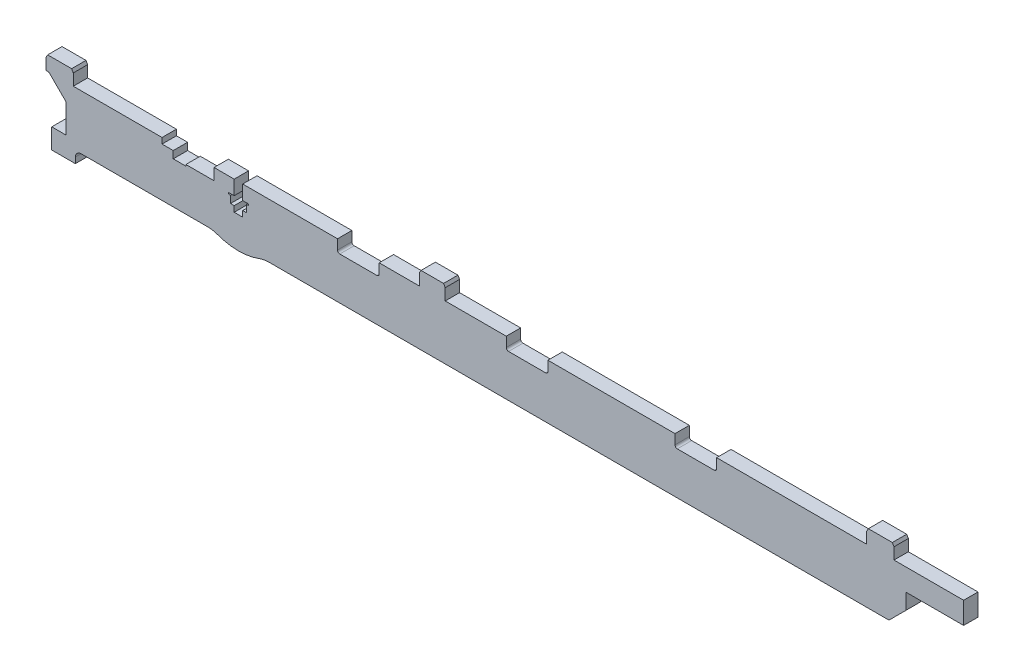
SolidWorks part; units mm, degrees
material "6061-T6 Black anodised"
ref_plane "Front Plane" through (0, 0, 0) normal (0, 0, 1) x (1, 0, 0)
ref_plane "Top Plane" through (0, 0, 0) normal (0, 1, 0) x (1, 0, 0)
ref_plane "Right Plane" through (0, 0, 0) normal (1, 0, 0) x (0, 0, -1)
sketch "Sketch1" plane through (0, 0, 0) normal (0, 0, 1) x (1, 0, 0)
  line L0 (-250.8, 3.6) -> (-241, 3.6)
  line L1 (0, 0) -> (20, 0)
  line L2 (-232.5, 8.6) -> (-232.5, -2.4) construction
  line L3 (-4.25, 7.6) -> (20, 7.6)
  line L4 (20, 0) -> (20, 7.6)
  line L5 (-13.75, 7.6) -> (-66, 7.6)
  line L6 (0, 0) -> (0, -11.4)
  line L7 (0, -11.4) -> (-221.7995, -11.4)
  line L8 (-292.5, 1.6) -> (-292.5, -8.4)
  line L9 (-259.0932, 7.6) -> (-290, 7.6)
  line L10 (-299.5, 7.6) -> (-299.5, 12.6)
  line L11 (-299.5, 12.6) -> (-290, 12.6)
  line L12 (-290, 7.6) -> (-290, 12.6)
  line L13 (-169.5, 7.6) -> (-169.5, 12.6)
  line L14 (-250.8, 3.6) -> (-250.8, 3.1)
  line L15 (-250.8, 3.1) -> (-255.2, 3.1)
  line L16 (-255.2, 3.1) -> (-255.2, 5.6)
  line L17 (-255.2, 5.6) -> (-259.0932, 5.6)
  line L18 (-4.25, 7.6) -> (-4.25, 12.6)
  line L19 (-4.25, 12.6) -> (-13.75, 12.6)
  line L20 (-13.75, 7.6) -> (-13.75, 12.6)
  line L21 (-259.0932, 5.6) -> (-259.0932, 7.6)
  line L22 (-255, 3.6) -> (-251, 3.6) construction
  line L23 (-255, 3.6) -> (-255, 13.6) construction
  line L24 (-251, 3.6) -> (-251, 13.6) construction
  line L25 (-255, 13.6) -> (-251, 13.6) construction
  line L26 (-255, 3.6) -> (-251, 13.6) construction
  line L27 (-271, 32.6) -> (-219.2068, 32.6) construction
  line L28 (-271, 32.6) -> (-271, 13.6) construction
  line L29 (-250, 33.6) -> (-250, 13.6) construction
  line L30 (-271, 13.6) -> (-250, 13.6) construction
  line L31 (-271, 32.6) -> (-250, 13.6) construction
  line L32 (-250, 33.6) -> (-271, 13.6) construction
  line L33 (-169.5, 12.6) -> (-160.5, 12.6)
  line L34 (-160.5, 12.6) -> (-160.5, 7.6)
  line L35 (-169.5, 7.6) -> (-183.5, 7.6)
  line L36 (-299.5, 7.6) -> (-298.5, 7.6)
  line L37 (-298.5, 7.6) -> (-292.5, 1.6)
  line L38 (-233.98, 7.6) -> (-233.98, 2.6)
  line L39 (-233.98, 2.6) -> (-236, 2.6)
  line L40 (-236, 2.6) -> (-236, 2.1)
  line L41 (-236, 2.1) -> (-235.25, 2.1)
  line L42 (-235.25, 2.1) -> (-235.25, -0.4)
  line L43 (-235.25, -0.4) -> (-233.98, -0.4)
  line L44 (-233.98, -0.4) -> (-233.98, -2.4)
  line L45 (-233.98, -2.4) -> (-231.02, -2.4)
  line L46 (-233.98, 7.6) -> (-241, 7.6)
  line L47 (-231.02, -0.4) -> (-231.02, -2.4)
  line L48 (-229.75, -0.4) -> (-231.02, -0.4)
  line L49 (-229.75, 2.1) -> (-229.75, -0.4)
  line L50 (-229, 2.1) -> (-229.75, 2.1)
  line L51 (-229, 2.6) -> (-229, 2.1)
  line L52 (-231.02, 2.6) -> (-229, 2.6)
  line L53 (-231.02, 7.6) -> (-231.02, 2.6)
  line L54 (-283, -20.0132) -> (-282, -18.2812)
  line L55 (-243.2005, -11.4) -> (-287.2708, -11.4)
  line L56 (-282, -15.4) -> (-287.2708, -15.4)
  line L57 (-251, 3.6) -> (-255, 13.6) construction
  line L58 (-282, -15.4) -> (-282, -18.2812)
  line L59 (-198, 7.6) -> (-231.02, 7.6)
  line L60 (-282, -30.9) -> (-297.5, -30.9)
  line L61 (-297.5, -30.9) -> (-297.5, -8.4)
  line L62 (-297.5, -8.4) -> (-292.5, -8.4)
  line L63 (-283, -25.7868) -> (-282, -27.5188)
  line L64 (-282, -23.9) -> (-282, -20.3633) construction
  line L65 (-283, -20.0132) -> (-286, -18.2812)
  line L66 (-286, -18.2812) -> (-290, -20.5906)
  line L67 (-290, -20.5906) -> (-290, -25.2094)
  line L68 (-290, -25.2094) -> (-286, -27.5188)
  line L69 (-286, -27.5188) -> (-283, -25.7868)
  line L70 (-282, -27.5188) -> (-282, -30.9)
  line L71 (-139.25, 7.6) -> (-160.5, 7.6)
  line L72 (-198, 7.6) -> (-198, 3.4)
  line L73 (-198, 3.4) -> (-183.5, 3.4)
  line L74 (-183.5, 7.6) -> (-183.5, 3.4)
  line L75 (-80.5, 7.6) -> (-124.75, 7.6)
  line L76 (-139.25, 7.6) -> (-139.25, 3.4)
  line L77 (-139.25, 3.4) -> (-124.75, 3.4)
  line L78 (-124.75, 7.6) -> (-124.75, 3.4)
  line L80 (-80.5, 7.6) -> (-80.5, 3.4)
  line L81 (-80.5, 3.4) -> (-66, 3.4)
  line L82 (-66, 7.6) -> (-66, 3.4)
  line L100 (-253, 8.6) -> (-238.8671, 8.6) construction
  line L116 (-241, 7.6) -> (-241, 3.6)
  arc A0 (-287.2708, -11.4) -> (-287.2708, -15.4) centre (-287.2708, -13.4) ccw
  circle A1 centre (-286, -22.9) radius 4 construction
  arc A2 (-221.7995, -11.4) -> (-225.2612, -12.0183) centre (-221.7995, -21.4) ccw
  arc A4 (-243.2005, -11.4) -> (-239.7388, -12.0183) centre (-243.2005, -21.4) cw
  arc A5 (-239.7388, -12.0183) -> (-225.2612, -12.0183) centre (-232.5, 7.6) ccw
  point P27 (-253, 8.6)
  point P130 (-242, 8.6)
  dimension "D21" = 0.5
  dimension "D24" = 0.5
  dimension "D26" = 2
  dimension "D34" = 8
  dimension "D35" = 2
  dimension "D39" = 10
  dimension "D40" = 9
  dimension "D2" = 20
  dimension "D3" = 7.6
  dimension "D4" = 5
  dimension "D5" = 11.4
  dimension "D6" = 1
  dimension "D7" = 9.5
  dimension "D8" = 6
  dimension "D9" = 6
  dimension "D10" = 6
  dimension "D11" = 4
  dimension "D12" = 9
  dimension "D13" = 189.5
  dimension "D14" = 10
  dimension "D15" = 4
  dimension "D16" = 1
  dimension "D17" = 8.5
  dimension "D18" = 20
  dimension "D19" = 42.5
  dimension "D20" = 25
  dimension "D22" = 0.2
  dimension "D23" = 0.2
  dimension "D25" = 2.5
  dimension "D27" = 2.96
  dimension "D28" = 11
  dimension "D29" = 7
  dimension "D30" = 5.5
  dimension "D31" = 270
  dimension "D32" = 11.5
  dimension "D33" = 6.5
  dimension "D36" = 5
  dimension "D37" = 8
  dimension "D38" = 16
  dimension "D41" = 13.75
  dimension "D42" = 14.5
  dimension "D43" = 58.75
  dimension "D44" = 58.75
  dimension "D45" = 1
  dimension "D46" = 52
  dimension "D47" = 4.2
extrude "Boss-Extrude1" add sketch "Sketch1" along normal blind 5
chamfer "Chamfer1" distance 6 angle 45 1 edges at (0, -11.4, 2.5)
chamfer "Chamfer2" [suppressed] distance 2.6 angle 60
sketch "Sketch2" plane through (-241, 0, 0) normal (-1, 0, 0) x (0, 0, 1)
  line L0 (5, 5.6) -> (2, 5.6) construction
  line L1 (5, 7.6) -> (5, 3.6) construction
  line L2 (2, 6.475) -> (2, 5.6) construction
  circle A0 centre (2, 5.6) radius 0.4645
extrude "Cut-Extrude1" [suppressed] cut sketch "Sketch2" against normal blind 0.5
sketch "Sketch3" plane through (0, 0, 5) normal (0, 0, 1) x (1, 0, 0)
  line L0 (-289.2708, -13.4) -> (-289.2708, -15.4)
  line L1 (-289.2708, -15.4) -> (-297.5, -15.4)
  line L2 (-282, -13.4) -> (-282, -30.9)
  line L3 (-282, -30.9) -> (-297.5, -30.9)
  line L4 (-297.5, -15.4) -> (-297.5, -30.9)
  line L5 (-289.2708, -13.4) -> (-282, -13.4)
  arc A0 (-287.2708, -11.4) -> (-287.2708, -15.4) centre (-287.2708, -13.4) ccw construction
extrude "Cut-Extrude2" cut sketch "Sketch3" against normal through all
chamfer "Chamfer3" distance 1 angle 30 3 edges at (-290, 12.6, 2.5) (-160.5, 12.6, 2.5) (-4.25, 12.6, 2.5)
chamfer "Chamfer4" distance 1 angle 30 3 edges at (-13.75, 12.6, 2.5) (-169.5, 12.6, 2.5) (-299.5, 12.6, 2.5)
fillet "Fillet1" radius 0.8 6 edges at (-66, 3.4, 2.5) (-80.5, 3.4, 2.5) (-124.75, 3.4, 2.5) (-139.25, 3.4, 2.5) (-183.5, 3.4, 2.5) (-198, 3.4, 2.5)
equation "\"y-plate-thickness\"=5"
equation "\"bed-plate-thickness\"=6"
equation "\"x-plate-thickness\"=5"
equation "\"rod-diameter\"=12"
equation "\"D4@Sketch1\"=\"x-plate-thickness\""
equation "\"D1@Boss-Extrude1\"=\"x-plate-thickness\""
equation "\"D44@Sketch1\"=\"D43@Sketch1\""
